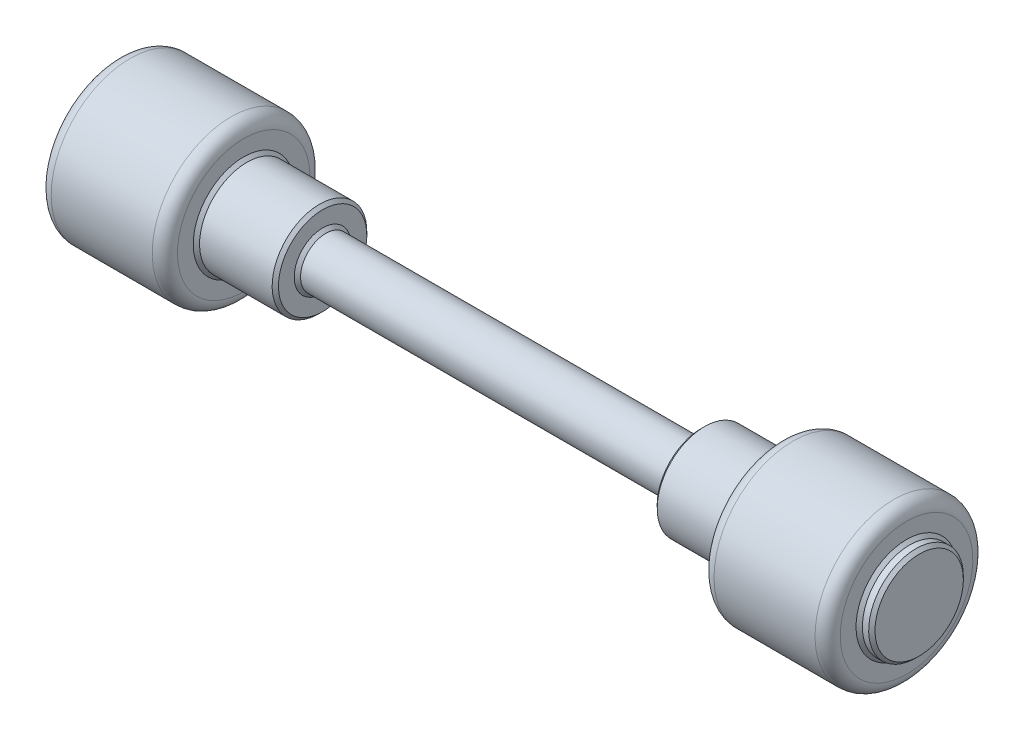
SolidWorks part; units mm, degrees
material "Balsa"
ref_plane "Front Plane" through (0, 0, 0) normal (0, 0, 1) x (1, 0, 0)
ref_plane "Top Plane" through (0, 0, 0) normal (0, 1, 0) x (1, 0, 0)
ref_plane "Right Plane" through (0, 0, 0) normal (1, 0, 0) x (0, 0, -1)
sketch "Sketch1" plane through (0, 0, 0) normal (0, 0, 1) x (1, 0, 0)
  line L0 (1612.5, 0) -> (-1612.5, 0)
  line L1 (-1612.5, 0) -> (-1612.5, 187.5)
  line L2 (-1612.5, 187.5) -> (-1562.5, 187.5)
  line L3 (-1562.5, 187.5) -> (-1562.5, 312.5)
  line L4 (-1562.5, 312.5) -> (-1062.5, 312.5)
  line L5 (-1062.5, 312.5) -> (-1062.5, 187.5)
  line L6 (-1062.5, 187.5) -> (-750, 187.5)
  line L7 (-750, 187.5) -> (-750, 100)
  line L8 (-750, 100) -> (750, 100)
  line L9 (750, 100) -> (750, 187.5)
  line L10 (750, 187.5) -> (1062.5, 187.5)
  line L11 (1062.5, 187.5) -> (1062.5, 312.5)
  line L12 (1062.5, 312.5) -> (1562.5, 312.5)
  line L13 (1562.5, 312.5) -> (1562.5, 187.5)
  line L14 (1562.5, 187.5) -> (1612.5, 187.5)
  line L15 (1612.5, 187.5) -> (1612.5, 0)
  point P4 (0, 0)
  dimension "D2" = 500
  dimension "D3" = 1500
  dimension "D4" = 50
  dimension "D5" = 312.5
  dimension "D6" = 187.5
  dimension "D7" = 312.5
  dimension "D8" = 187.5
  dimension "D9" = 100
  dimension "D10" = 187.5
  dimension "D11" = 187.5
revolve "Revolve1" add sketch "Sketch1" angle 360 about L0
chamfer "Chamfer1" distance 12.5 angle 45 10 edges at (-1562.5, 187.5, 0) (-1612.5, 187.5, 0) (1612.5, 187.5, 0) (1562.5, 187.5, 0) (750, 100, 0) (-750, 100, 0) (1062.5, 187.5, 0) (750, 187.5, 0) (-750, 187.5, 0) (-1062.5, 187.5, 0)
fillet "Fillet1" radius 50 4 edges at (1562.5, 312.5, 0) (1062.5, 312.5, 0) (-1062.5, 312.5, 0) (-1562.5, 312.5, 0)
